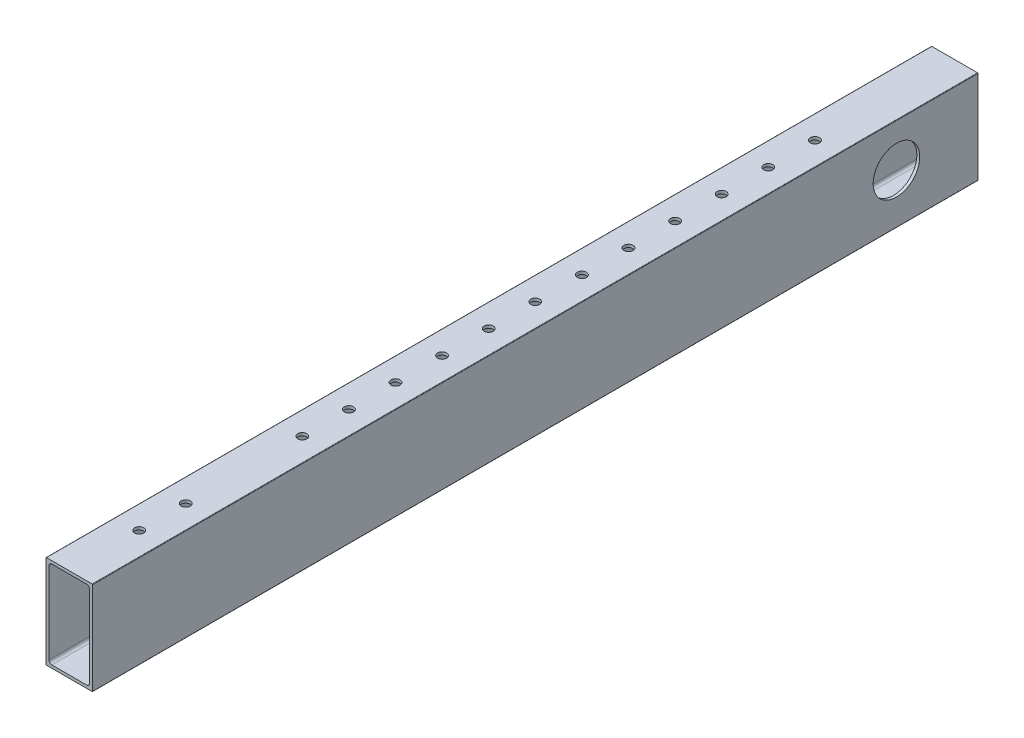
SolidWorks part; units mm, degrees
material "6061 Alloy"
ref_plane "Front Plane" through (0, 0, 0) normal (0, 0, 1) x (1, 0, 0)
ref_plane "Top Plane" through (0, 0, 0) normal (0, 1, 0) x (1, 0, 0)
ref_plane "Right Plane" through (0, 0, 0) normal (1, 0, 0) x (0, 0, -1)
ref_plane "Plane1" through (0, 0, 0) normal (0, 0, -1) x (-1, 0, 0)
sketch "Sketch1" plane through (0, 0, 0) normal (0, 0, -1) x (-1, 0, 0)
  line L0 (-11.1125, -22.225) -> (-11.1125, 22.225)
  line L1 (-9.525, 23.8125) -> (9.525, 23.8125)
  line L2 (11.1125, 22.225) -> (11.1125, -22.225)
  line L3 (9.525, -23.8125) -> (-9.525, -23.8125)
  line L4 (-12.7, 25.146) -> (-12.7, -25.146)
  line L5 (-12.446, -25.4) -> (12.446, -25.4)
  line L6 (12.7, -25.146) -> (12.7, 25.146)
  line L7 (12.446, 25.4) -> (-12.446, 25.4)
  arc A0 (-11.1125, 22.225) -> (-9.525, 23.8125) centre (-9.525, 22.225) cw
  arc A1 (9.525, 23.8125) -> (11.1125, 22.225) centre (9.525, 22.225) cw
  arc A2 (11.1125, -22.225) -> (9.525, -23.8125) centre (9.525, -22.225) cw
  arc A3 (-9.525, -23.8125) -> (-11.1125, -22.225) centre (-9.525, -22.225) cw
  arc A4 (-12.7, -25.146) -> (-12.446, -25.4) centre (-12.446, -25.146) ccw
  arc A5 (12.446, -25.4) -> (12.7, -25.146) centre (12.446, -25.146) ccw
  arc A6 (12.7, 25.146) -> (12.446, 25.4) centre (12.446, 25.146) ccw
  arc A7 (-12.446, 25.4) -> (-12.7, 25.146) centre (-12.446, 25.146) ccw
extrude "Boss-Extrude1" add sketch "Sketch1" against normal blind 457.2 and the other way blind 25.4
sketch "Sketch2" plane through (-12.7, 0, 0) normal (-1, 0, 0) x (0, 0, 1)
  line L0 (0, 1.778) -> (19.05, 1.778) construction
  line L1 (0, 25.146) -> (0, -25.146) construction
  line L8 (-25.4, 25.146) -> (457.2, 25.146) construction
  line L9 (-25.4, -25.146) -> (457.2, -25.146) construction
  line L10 (-25.4, -25.4) -> (457.2, -25.4) construction
  circle A0 centre (19.05, 1.778) radius 12.7
  dimension "D3" = 27.178
  dimension "D2" = 25.4
  dimension "D1" = 19.05
extrude "Cut-Extrude1" cut sketch "Sketch2" against normal blind 25.4
sketch "Sketch3" plane through (0, -25.4, 0) normal (0, -1, 0) x (1, 0, 0)
  line L0 (0, 0) -> (0, 457.2) construction
  line L1 (12.446, 457.2) -> (-12.446, 457.2) construction
  line L2 (12.446, -25.4) -> (-12.446, -25.4) construction
  line L3 (-12.7, 355.6) -> (12.7, 355.6) construction
  line L4 (-12.7, 457.2) -> (-12.7, -25.4) construction
  line L5 (12.7, 457.2) -> (12.7, -25.4) construction
  circle A0 centre (0, 50.8) radius 2.4892
  circle A1 centre (0, 76.2) radius 2.4892
  circle A2 centre (0, 101.6) radius 2.4892
  circle A3 centre (0, 127) radius 2.4892
  circle A4 centre (0, 152.4) radius 2.4892
  circle A5 centre (0, 177.8) radius 2.4892
  circle A6 centre (0, 203.2) radius 2.4892
  circle A7 centre (0, 228.6) radius 2.4892
  circle A8 centre (0, 254) radius 2.4892
  circle A9 centre (0, 279.4) radius 2.4892
  circle A10 centre (0, 304.8) radius 2.4892
  circle A11 centre (0, 393.7) radius 2.4892
  circle A12 centre (0, 419.1) radius 2.4892
  circle A13 centre (0, 330.2) radius 2.4892
  dimension "D1" = 76.2
  dimension "D2" = 4.9784
  dimension "D3" = 12
  dimension "D4" = 25.4
  dimension "D7" = 127
  dimension "D5" = 38.1
  dimension "D6" = 101.6
extrude "Cut-Extrude2" cut sketch "Sketch3" against normal through all both
